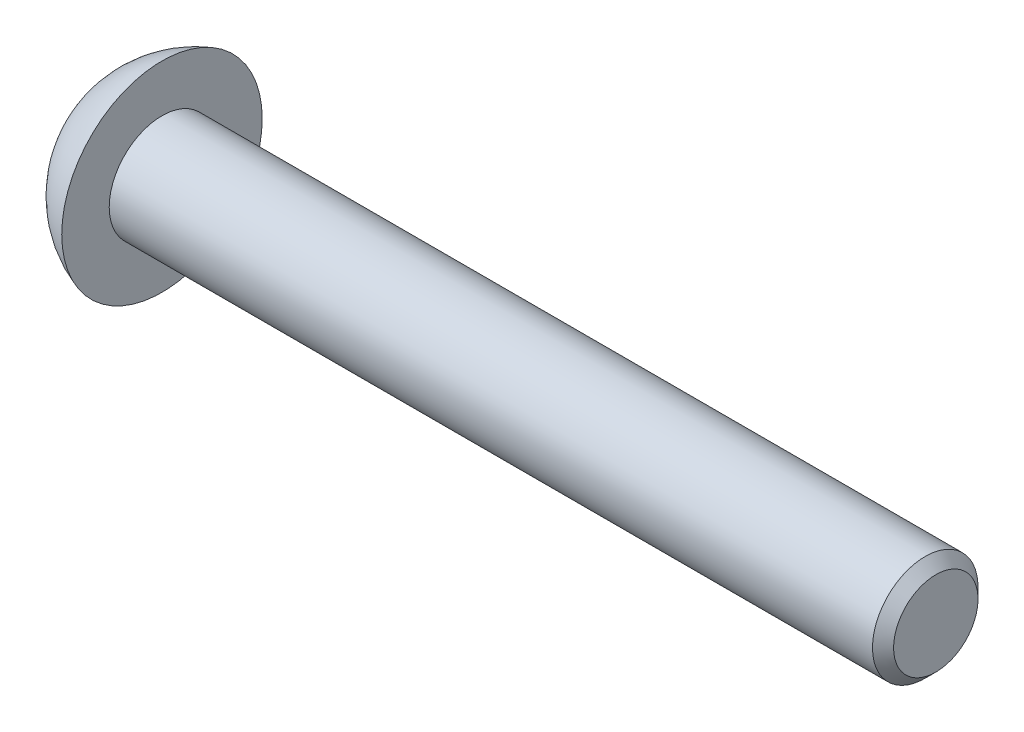
SolidWorks part; units mm, degrees
ref_plane "Front Plane" through (0, 0, 0) normal (0, 0, 1) x (1, 0, 0)
ref_plane "Top Plane" through (0, 0, 0) normal (0, 1, 0) x (1, 0, 0)
ref_plane "Right Plane" through (0, 0, 0) normal (1, 0, 0) x (0, 0, -1)
sketch "Sketch1" plane through (0, 0, 0) normal (0, 1, 0) x (1, 0, 0)
  line L0 (0, 1.5) -> (0, 4.35)
  line L1 (0, 0) -> (22, 0)
  line L2 (0, 0) -> (0, 3)
  line L3 (0, 3) -> (22, 3)
  line L4 (22, 0) -> (22, 3)
  line L5 (0, 1.5) -> (-1.65, 1.5)
  line L6 (-1.65, 1.5) -> (-1.65, 2.5)
  line L7 (-1.65, 2.5) -> (-1.65, 3)
  line L8 (0, 1.5) -> (22, 1.5)
  circle A0 centre (0.9455, 1.511) radius 2.9923
  dimension "D1" = 22
  dimension "D2" = 3
  dimension "D3" = 2.85
  dimension "D4" = 1.65
  dimension "D5" = 1
  dimension "D6" = 0.5
revolve "Revolve1" add sketch "Sketch1" angle 360 about L8
chamfer "Chamfer1" distance 0.3 angle 45 1 edges at (22, 0, 0)
sketch "Sketch2" plane through (-1.65, 0, 0) normal (-1, 0, 0) x (0, 0, 1)
  line L1 (-0.3453, 0) -> (-0.9226, 1)
  line L2 (-0.9226, 1) -> (-2.0774, 1)
  line L3 (-2.0774, 1) -> (-2.6547, 0)
  line L4 (-2.6547, 0) -> (-2.0774, -1)
  line L5 (-2.0774, -1) -> (-0.9226, -1)
  line L6 (-0.9226, -1) -> (-0.3453, 0)
  circle A0 centre (-1.5, 0) radius 1 construction
  circle A1 centre (-1.5, 0) radius 1.5
  circle A2 centre (-1.5, 0) radius 1.5
  dimension "D2" = 2
  dimension "D1" = 0
extrude "Cut-Extrude1" cut sketch "Sketch2" against normal blind 1.2 contours L1 L2 L3 L4 L5 L6
